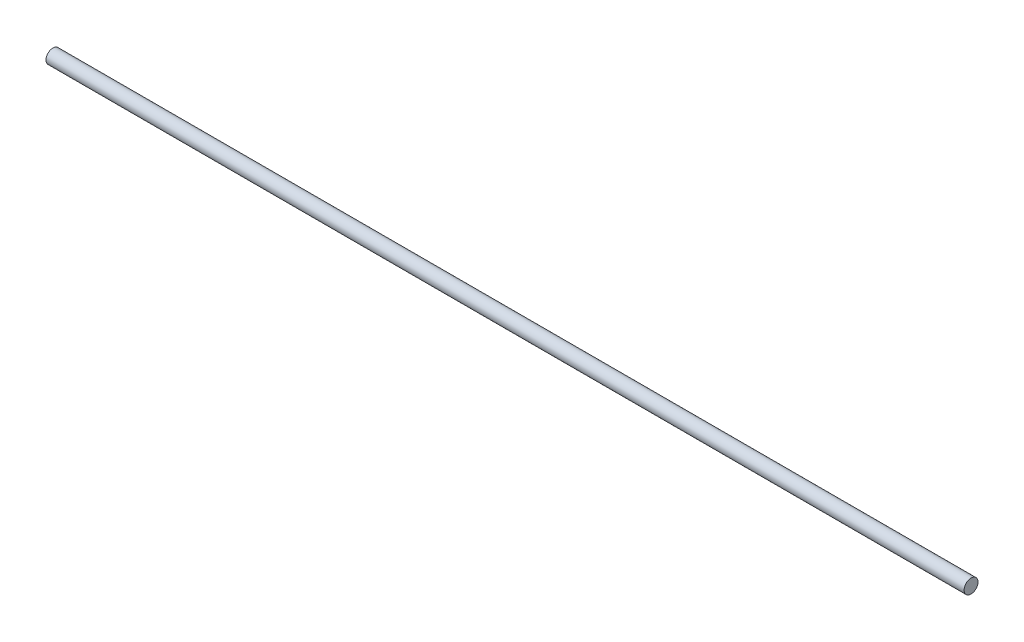
SolidWorks part; units mm, degrees
ref_plane "Front Plane" through (0, 0, 0) normal (0, 0, 1) x (1, 0, 0)
ref_plane "Top Plane" through (0, 0, 0) normal (0, 1, 0) x (1, 0, 0)
ref_plane "Right Plane" through (0, 0, 0) normal (1, 0, 0) x (0, 0, -1)
sketch "Sketch1" plane through (0, 0, 0) normal (0, 0, 1) x (1, 0, 0)
  line L0 (-0.6743, 0.1171) -> (-288.5623, 0.1171) construction
  line L1 (-0.6743, 0.1171) -> (-25.6743, 0.1171) construction
  line L2 (-2.4771, 2.1171) -> (-25.6743, 2.1171) construction
  line L3 (-2.4771, -1.8829) -> (-25.6743, -1.8829) construction
  line L4 (-25.6743, 2.1171) -> (-25.6743, -1.8829) construction
  line L5 (-0.6743, 2.1171) -> (-25.6743, 2.1171) construction
  line L6 (-0.6743, -1.8829) -> (-25.6743, -1.8829) construction
  line L7 (-14.1743, 0.1171) -> (-0.6743, 0.1171) construction
  line L8 (-288.5623, 0.1171) -> (-278.0623, 0.1171) construction
  circle A0 centre (-0.6743, 0.1171) radius 1 construction
  arc A1 (-1.962, -2.0257) -> (-1.962, 2.26) centre (-0.6743, 0.1171) ccw construction
  arc A2 (-2.4771, 2.1171) -> (-1.962, 2.26) centre (-2.4771, 3.1171) ccw construction
  arc A3 (-2.4771, -1.8829) -> (-1.962, -2.0257) centre (-2.4771, -2.8829) cw construction
  circle A4 centre (-0.6743, 0.1171) radius 13.5 construction
  circle A5 centre (-288.5623, 0.1171) radius 10.5 construction
  dimension "D1" = 2
  dimension "D3" = 1
  dimension "D4" = 1
  dimension "D2" = 2
  dimension "D5" = 287.888
sketch "Sketch2" plane through (0, 0, 0) normal (1, 0, 0) x (0, 0, -1)
  line L0 (0, 13.6171) -> (0, -13.3829) construction
  circle A0 centre (0, 0.1171) radius 2
extrude "Boss-Extrude1" add sketch "Sketch2" against normal up to vertex (278.0623 mm away) from vertex at -14.1743 contours A0 starting at point (-14.1743, 0.1171, 0)
